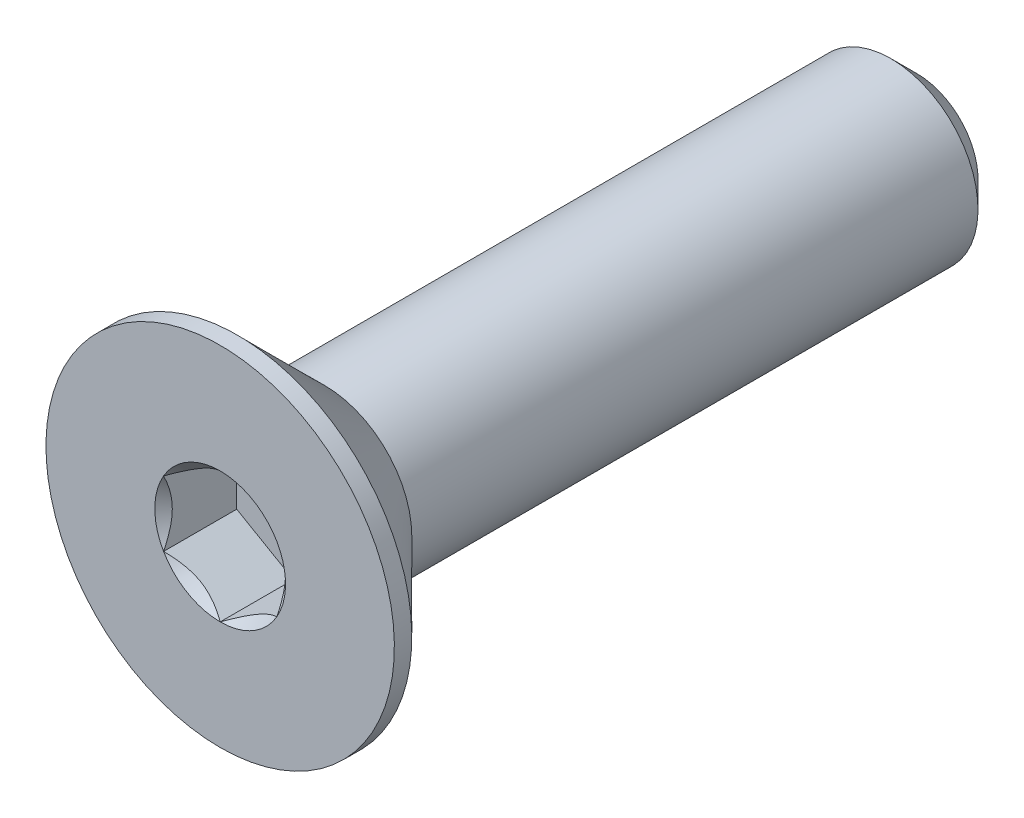
SolidWorks part; units mm, degrees
ref_plane "Front" through (0, 0, 0) normal (0, 0, 1) x (1, 0, 0)
ref_plane "Top" through (0, 0, 0) normal (0, 1, 0) x (1, 0, 0)
ref_plane "Right" through (0, 0, 0) normal (1, 0, 0) x (0, 0, -1)
sketch "Sketch1" plane through (0, 0, 0) normal (1, 0, 0) x (0, 0, -1)
  line L0 (0, 2) -> (0.2, 2) construction
  line L1 (0.2, 2) -> (1.2, 1) construction
  line L2 (0, 1) -> (8, 1)
  line L3 (8, 1) -> (8, 0)
  line L4 (8, 0) -> (0, 0)
  line L5 (0, 0) -> (0, 2) construction
  line L6 (0, 2) -> (0, -2) construction
  line L7 (8, 1) -> (8, -1) construction
  line L8 (0, -2) -> (0.2, -2) construction
  line L9 (0.2, -2) -> (1.2, -1) construction
  line L11 (0, 1) -> (0, 0)
  line L12 (1.2, 1) -> (1.2, 0) construction
  dimension "Head Ht" = 1.2
  dimension "Head Dia" = 4
  dimension "Dia" = 2
  dimension "Lg" = 8
  dimension "Head Angle" = 90
revolve "Revolve1" add sketch "Sketch1" angle 360 mid plane about L4
sketch "Sketch3" plane through (0, 0, -8) normal (0, 0, -1) x (-1, 0, 0)
  circle A0 centre (0, 0) radius 1
curve "Helix/Spiral1" pitch 0.4 height 8 turns 20
sketch "Sketch2" plane through (0, 0, 0) normal (1, 0, 0) x (0, 0, -1)
  line L0 (8, 1) -> (8.35, 1)
  line L1 (8.35, 1) -> (8.2, 0.7402)
  line L2 (8.2, 0.7402) -> (8.15, 0.7402)
  line L3 (8.15, 0.7402) -> (8, 1)
  line L4 (8.075, 0.8701) -> (8.275, 0.8701) construction
  dimension "D1" = 60
  dimension "D2" = 0.05
  dimension "D3" = 0.2
chamfer "Chamfer1" distance 0.3 angle 45 1 edges at (0, 1, -8)
sketch "Sketch7" plane through (0, 0, 0) normal (1, 0, 0) x (0, 0, -1)
  line L0 (0, 2) -> (0.2, 2) construction
  line L1 (0.2, 2) -> (1.2, 1) construction
  line L2 (0, 2) -> (0.2, 2)
  line L3 (0.2, 2) -> (1.2, 1)
  line L4 (1.2, 1) -> (1.2, 0) construction
  line L5 (1.2, 1) -> (1.2, 0)
  line L7 (0, 0) -> (0, 2) construction
  line L8 (0, 0) -> (0, 2)
  line L9 (0, 0) -> (1.2, 0)
  line L10 (2.2, 0) -> (-2.2, 0) construction
revolve "Revolve2" add sketch "Sketch7" angle 360 mid plane about L9
ref_plane "Plane1" through (0, 0, -1.2) normal (0, 0, 1) x (1, 0, 0)
sketch "Sketch8" plane through (0, 0, -1.2) normal (0, 0, 1) x (1, 0, 0)
  circle A0 centre (0, 0) radius 1
extrude "Boss-Extrude1" add sketch "Sketch8" against normal through all draft 45
sketch "Sketch5" plane through (0, 0, 0) normal (0, 0, 1) x (1, 0, 0)
  line L1 (0.65, -0.3753) -> (0.65, 0.3753)
  line L2 (0.65, 0.3753) -> (0, 0.7506)
  line L3 (0, 0.7506) -> (-0.65, 0.3753)
  line L4 (-0.65, 0.3753) -> (-0.65, -0.3753)
  line L5 (-0.65, -0.3753) -> (0, -0.7506)
  line L6 (0, -0.7506) -> (0.65, -0.3753)
  circle A0 centre (0, 0) radius 0.65 construction
  dimension "Hex" = 1.3
extrude "Cut-Extrude2" cut sketch "Sketch5" against normal blind 0.84
sketch "Sketch6" plane through (0, 0, 0) normal (0, 0, 1) x (1, 0, 0)
  circle A0 centre (0, 0) radius 0.7506
extrude "Cut-Extrude3" cut sketch "Sketch6" against normal blind 0.84 draft 45
sketch "Sketch9" [suppressed] plane through (0, 0, -5.5) normal (0, 0, 1) x (1, 0, 0)
  circle A1 centre (0, 0) radius 5
  circle A2 centre (0, 0) radius 5
  point P0 (0, 5)
  dimension "D1" = 0
extrude "Boss-Extrude2" [suppressed] add sketch "Sketch9" against normal offset from surface (18.5 mm away) 26
fillet "Fillet1" [suppressed] radius 0.2
sketch "Sketch10" plane through (0, 0, 0) normal (1, 0, 0) x (0, 0, -1)
  line L0 (8, 1) -> (8, -1) construction
  point P0 (7.4, -1)
  dimension "D1" = 0.6
equation "\"D3@Helix/Spiral1\" = \"Lg@Sketch1\""
equation "\"D2@Sketch2\" = \"D4@Helix/Spiral1\" * .125"
equation "\"D3@Sketch2\" = \"D4@Helix/Spiral1\" * .5"
equation "\"D1@Chamfer1\" = \"D4@Helix/Spiral1\" * .75"
equation "\"D1@Cut-Extrude2\" = \"Head Ht@Sketch1\" * .7"
equation "\"D1@Sketch10\" = \"D4@Helix/Spiral1\" * 1.5"
equation "\"D1@Cut-Extrude3\" = \"D1@Cut-Extrude2\""
equation "\"D1@Fillet1\" = \"Dia@Sketch1\" * .1"
